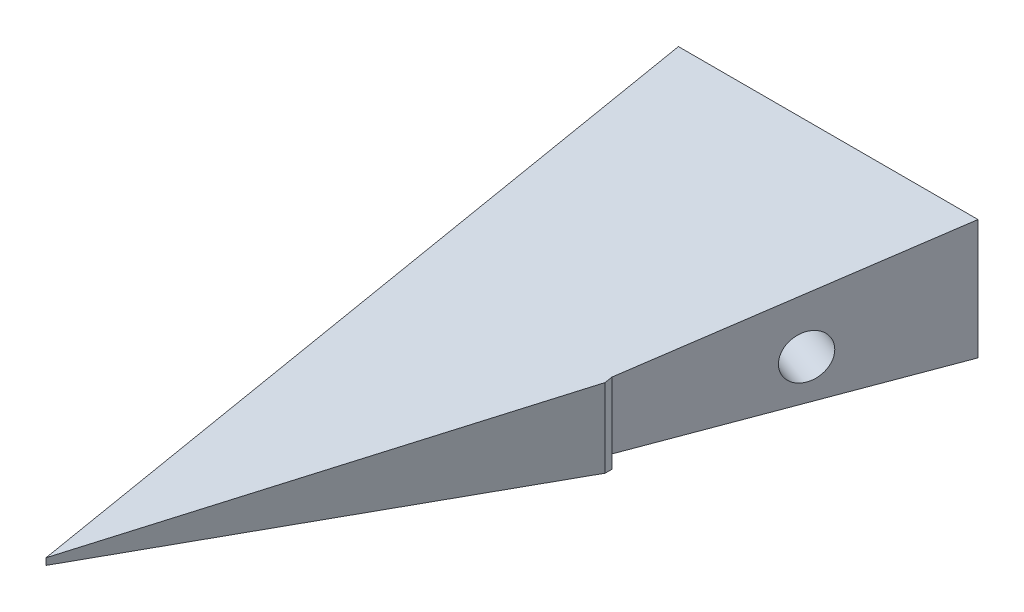
SolidWorks part; units mm, degrees
material "AISI 1020"
ref_plane "Plano frontal" through (0, 0, 0) normal (0, 0, 1) x (1, 0, 0)
ref_plane "Plano superior" through (0, 0, 0) normal (0, 1, 0) x (1, 0, 0)
ref_plane "Plano direito" through (0, 0, 0) normal (1, 0, 0) x (0, 0, -1)
sketch "Esboço1" plane through (0, 0, 0) normal (0, 0, 1) x (1, 0, 0)
  line L1 (-65, 10) -> (65, 10)
  line L2 (-65, 10) -> (-65, -10)
  line L3 (-65, -10) -> (65, -10)
  line L4 (65, 10) -> (65, -10)
  line L5 (-65, 10) -> (65, -10) construction
  line L6 (-65, -10) -> (65, 10) construction
  point P0 (0, 0)
  dimension "D1" = 130
  dimension "D2" = 20
extrude "Ressalto-extrusão1" add sketch "Esboço1" along normal blind 95
sketch "Esboço2" plane through (0, 10, 0) normal (0, 1, 0) x (1, 0, 0)
  line L0 (65, 0) -> (-20, 0)
  line L2 (-65, -95) -> (-65, 0) construction
  line L3 (-35, -40) -> (-20, 0)
  line L4 (65, 0) -> (-65, 0) construction
  line L9 (-35, -40) -> (-35, -41)
  line L12 (65, -95) -> (65, 0)
  line L17 (-35, -41) -> (-65, -95)
  line L18 (-65, -95) -> (65, -95)
  dimension "D5" = 1
  dimension "D1" = 45
  dimension "D2" = 30
  dimension "D4" = 40
extrude "Corte-extrusão2" cut sketch "Esboço2" against normal up to next contours L3 L0 L12 L18 L17 L9
sketch "Esboço13" plane through (-65, 0, 0) normal (-1, 0, 0) x (0, 0, 1)
  line L0 (0, 10) -> (95, -9)
  line L1 (95, 10) -> (95, -10) construction
  dimension "D1" = 1
extrude "Corte-extrusão4" cut sketch "Esboço13" against normal through all and the other way through all
hole_wizard "Broca de rosquear de cano para tarraxa de 1/84" positions "Esboço14" profile "Esboço15" hole size "1/8" standard "Ansi Inch"
sketch "Esboço14" plane through (-65, 0, 0) normal (-1, 0, 0) x (0, 0, 1)
  line L0 (0, 10) -> (0, -10) construction
  line L1 (95, -10) -> (0, -10) construction
  point P0 (20, -2)
  dimension "D1" = 20
  dimension "D2" = 8
sketch "Esboço15" plane through (-65, -2, 20) normal (0, 1, 0) x (0, 0, 1)
  line L0 (0, 0) -> (0, 11.9768)
  line L1 (0, 11.9768) -> (3.29, 10)
  line L2 (3.29, 10) -> (3.29, 0)
  line L5 (3.29, 0) -> (0, 0)
  line L10 (0, 11.9768) -> (-3.29, 10) construction
  line L11 (0, -6.35) -> (0, 107.95) construction
  dimension "Hole Dia." = 6.58
  dimension "Hole Depth" = 10
  dimension "Drill Angle" = 118
hole_wizard "Broca de rosquear de cano para tarraxa de 1/85" positions "Esboço16" profile "Esboço17" hole size "1/8" standard "Ansi Inch"
sketch "Esboço16" plane through (-17.5342, 0, -6.5753) normal (0.9363, 0, 0.3511) x (0.3511, 0, -0.9363)
  line L0 (-7.0225, -10) -> (-7.0225, 10) construction
  line L1 (-7.0225, -10) -> (-49.7425, -10) construction
  point P0 (-27.0225, -2)
  dimension "D1" = 20
  dimension "D2" = 8
sketch "Esboço17" plane through (-27.0225, -2, 18.7266) normal (0, 1, 0) x (0.3511, 0, -0.9363)
  line L0 (0, 0) -> (0, 11.9768)
  line L1 (0, 11.9768) -> (3.29, 10)
  line L2 (3.29, 10) -> (3.29, 0)
  line L5 (3.29, 0) -> (0, 0)
  line L10 (0, 11.9768) -> (-3.29, 10) construction
  line L11 (0, -6.35) -> (0, 107.95) construction
  dimension "Hole Dia." = 6.58
  dimension "Hole Depth" = 10
  dimension "Drill Angle" = 118
sketch "Esboço42" plane through (0, 0, 0) normal (0, 0, -1) x (-1, 0, 0)
  line L0 (20, -10) -> (20, -8)
  line L1 (20, -8) -> (65, -8)
  line L2 (65, 10) -> (65, -10) construction
  line L3 (65, -8) -> (65, -10)
  line L4 (65, -10) -> (20, -10)
  dimension "D1" = 2
extrude "Corte-extrusão5" cut sketch "Esboço42" against normal up to vertex (40 mm away) up to point (-35, -10, 40)
